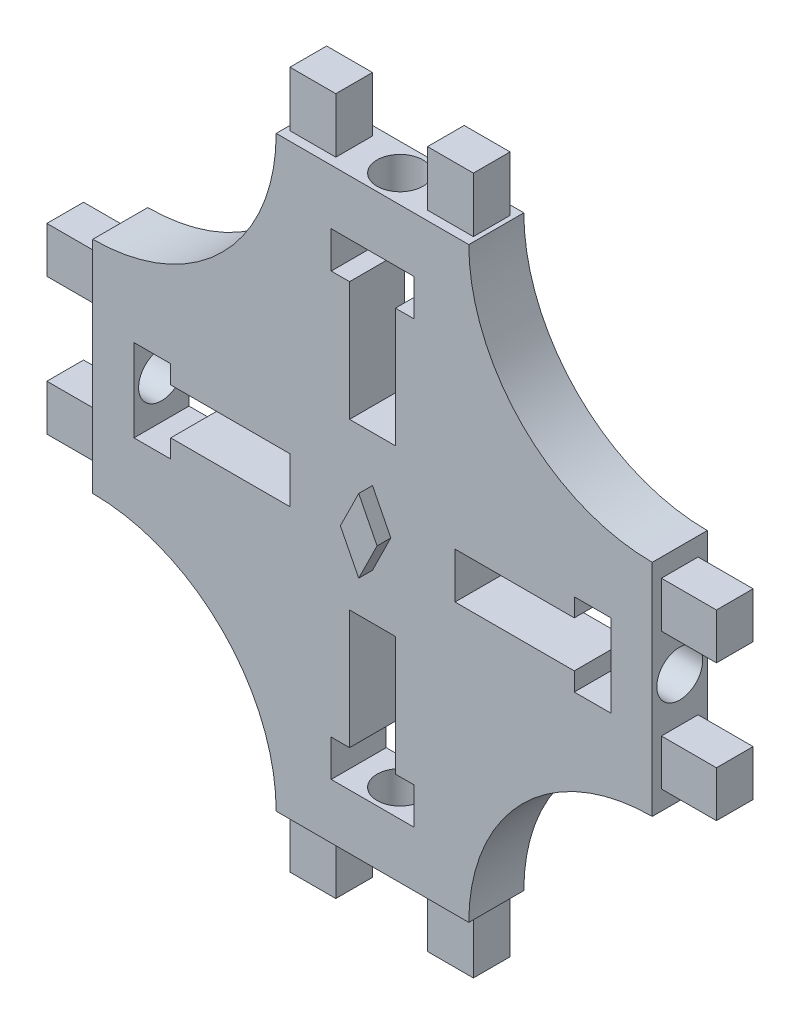
SolidWorks part; units mm, degrees
ref_plane "前视基准面" through (0, 0, 0) normal (0, 0, 1) x (1, 0, 0)
ref_plane "上视基准面" through (0, 0, 0) normal (0, 1, 0) x (1, 0, 0)
ref_plane "右视基准面" through (0, 0, 0) normal (1, 0, 0) x (0, 0, -1)
sketch "草图1" plane through (0, 0, 0) normal (0, 0, 1) x (1, 0, 0)
  line L0 (-15.25, 0) -> (15.25, 0) construction
  line L1 (-5, -16) -> (5, -16)
  line L2 (-15.25, -5) -> (-15.25, 5)
  line L3 (-5, 16) -> (5, 16)
  line L4 (15.25, -5) -> (15.25, 5)
  line L5 (-7.7137, -8.093) -> (7.7137, 8.093) construction
  line L6 (-7.7137, 8.093) -> (7.7137, -8.093) construction
  line L7 (0, 16) -> (0, -16) construction
  line L8 (-15.25, 0) -> (-15.25, 5)
  line L9 (-15.25, 0) -> (-15.25, -5)
  line L10 (0, 16) -> (-5, 16)
  line L11 (0, 16) -> (5, 16)
  line L12 (-2.25, 13) -> (0, 13)
  line L13 (0, -16) -> (-5, -16)
  line L14 (0, -16) -> (5, -16)
  line L15 (15.25, 0) -> (15.25, 5)
  line L16 (15.25, 0) -> (15.25, -5)
  line L17 (0, 13) -> (2.25, 13)
  line L18 (-2.25, 13) -> (-2.25, 11)
  line L19 (-2.25, 11) -> (2.25, 11)
  line L20 (2.25, 11) -> (2.25, 13)
  line L21 (-1.25, 11) -> (-1.25, 4.5)
  line L22 (-1.25, 4.5) -> (1.25, 4.5)
  line L23 (1.25, 4.5) -> (1.25, 11)
  line L24 (-1.25, -4.5) -> (1.25, -4.5)
  line L25 (-1.25, -11) -> (-1.25, -4.5)
  line L26 (1.25, -4.5) -> (1.25, -11)
  line L27 (-2.25, -11) -> (2.25, -11)
  line L28 (2.25, -11) -> (2.25, -13)
  line L29 (0, -13) -> (2.25, -13)
  line L30 (-2.25, -13) -> (0, -13)
  line L31 (-2.25, -13) -> (-2.25, -11)
  line L32 (4.5, 1.25) -> (11, 1.25)
  line L33 (4.5, -1.25) -> (4.5, 1.25)
  line L34 (11, -1.25) -> (4.5, -1.25)
  line L35 (11, -2.25) -> (11, 2.25)
  line L36 (13, -2.25) -> (11, -2.25)
  line L37 (11, 2.25) -> (13, 2.25)
  line L38 (13, 0) -> (13, 2.25)
  line L39 (13, -2.25) -> (13, 0)
  line L40 (-13, -2.25) -> (-13, 0)
  line L41 (-13, 0) -> (-13, 2.25)
  line L42 (-11, 2.25) -> (-13, 2.25)
  line L43 (-13, -2.25) -> (-11, -2.25)
  line L44 (-11, -2.25) -> (-11, 2.25)
  line L45 (-11, -1.25) -> (-4.5, -1.25)
  line L46 (-4.5, -1.25) -> (-4.5, 1.25)
  line L47 (-4.5, 1.25) -> (-11, 1.25)
  line L48 (-15.25, 5) -> (-15.25, 6)
  line L49 (-5.25, 16) -> (-5, 16)
  line L50 (5, 16) -> (5.25, 16)
  line L51 (15.25, 6) -> (15.25, 5)
  line L52 (15.25, -5) -> (15.25, -6)
  line L53 (5.25, -16) -> (5, -16)
  line L54 (-5, -16) -> (-5.25, -16)
  line L55 (-15.25, -6) -> (-15.25, -5)
  line L56 (-15.25, 5) -> (-15.25, 6)
  line L57 (-5, 16) -> (-5.25, 16)
  line L58 (5, 16) -> (5.25, 16)
  line L59 (15.25, 5) -> (15.25, 6)
  line L60 (15.25, -6) -> (15.25, -5)
  line L61 (5, -16) -> (5.25, -16)
  line L62 (-5, -16) -> (-5.25, -16)
  line L63 (-15.25, -5) -> (-15.25, -6)
  arc A4 (-15.25, 6) -> (-5.25, 16) centre (-15.25, 16) ccw
  arc A5 (5.25, 16) -> (15.25, 6) centre (15.25, 16) ccw
  arc A6 (15.25, -6) -> (5.25, -16) centre (15.25, -16) ccw
  arc A7 (-5.25, -16) -> (-15.25, -6) centre (-15.25, -16) ccw
  point P0 (0, 0)
  point P51 (0, 0)
  dimension "D11" = 20
  dimension "D19" = 20
  dimension "D20" = 20
  dimension "D21" = 20
  dimension "D2" = 32
  dimension "D3" = 5
  dimension "D4" = 5
  dimension "D5" = 5
  dimension "D6" = 5
  dimension "D7" = 5
  dimension "D8" = 5
  dimension "D9" = 5
  dimension "D10" = 5
  dimension "D12" = 30.5
  dimension "D13" = 2.25
  dimension "D14" = 2
  dimension "D15" = 3
  dimension "D16" = 2.5
  dimension "D17" = 6.5
  dimension "D18" = 2
extrude "凸台-拉伸2" add sketch "草图1" along normal blind 3
sketch "草图2" plane through (0, 16, 0) normal (0, 1, 0) x (1, 0, 0)
  line L0 (-5.25, 0) -> (5.25, -3) construction
  line L1 (5.25, 0) -> (-5.25, -3) construction
  circle A0 centre (0, -1.5) radius 1.25
  point P10 (0, 0)
  point P11 (0, 0)
  point P12 (-5.25, 0)
  point P14 (-5.25, -3)
  point P16 (5.25, 0)
  point P18 (5.25, -3)
  dimension "D1" = 2.5
extrude "切除-拉伸1" cut sketch "草图2" against normal blind 4
pattern_circular "阵列(圆周)1" count 4 over 360 about axis through (0, 0, 3) along (0, 0, 1) of "切除-拉伸1"
sketch "草图3" plane through (0, 0, 3) normal (0, 0, 1) x (1, 0, 0)
  line L0 (0, 0) -> (0, 2)
  line L1 (0, 0) -> (0, -2)
  line L2 (-1, -0.0251) -> (0, -2)
  line L3 (-1, -0.0251) -> (0, 2)
  line L4 (0, 2) -> (1, 0.0251)
  line L5 (1, 0.0251) -> (0, -2)
  line L6 (-1, -0.0251) -> (0, 0)
  line L7 (1, 0.0251) -> (0, 0)
  dimension "D1" = 1
  dimension "D2" = 2
extrude "凸台-拉伸3" add sketch "草图3" along normal blind 0.75 contours L7 L4 L0 | L3 L6 L0 | L6 L2 L1 | L5 L7 L1
sketch "草图4" plane through (0, 16, 0) normal (0, 1, 0) x (1, 0, 0)
  line L0 (0, -3.75) -> (0, -3) construction
  line L1 (2.5, -2.5) -> (5, -2.5)
  line L2 (2.5, -2.5) -> (2.5, -0.5)
  line L3 (2.5, -0.5) -> (5, -0.5)
  line L4 (5, -2.5) -> (5, -0.5)
  line L5 (2.5, -2.5) -> (5, -0.5) construction
  line L6 (2.5, -0.5) -> (5, -2.5) construction
  line L7 (-2.5, -2.5) -> (-5, -2.5)
  line L8 (-5, -2.5) -> (-5, -0.5)
  line L9 (-2.5, -2.5) -> (-2.5, -0.5)
  line L10 (-2.5, -0.5) -> (-5, -0.5)
  circle A0 centre (0, -1.5) radius 1.25 construction
  circle A1 centre (0, -1.5) radius 1.25
  point P3 (3.75, -1.5)
  point P8 (0, 0)
  dimension "D1" = 3.75
  dimension "D2" = 2
  dimension "D3" = 2.5
extrude "凸台-拉伸5" add sketch "草图4" along normal blind 3
pattern_linear "阵列(线性)1" count 2 spacing 35 along (0, -1, 0) of "凸台-拉伸5"
sketch "草图5" plane through (15.25, 0, 0) normal (1, 0, 0) x (0, 0, -1)
  line L0 (-3.75, 0.0251) -> (-3, 0.0251) construction
  line L1 (-2.5, 2.5) -> (-0.5, 2.5)
  line L2 (-2.5, 2.5) -> (-2.5, 5)
  line L3 (-2.5, 5) -> (-0.5, 5)
  line L4 (-0.5, 2.5) -> (-0.5, 5)
  line L5 (-2.5, 2.5) -> (-0.5, 5) construction
  line L6 (-2.5, 5) -> (-0.5, 2.5) construction
  line L7 (-2.5, -2.4498) -> (-0.5, -2.4498)
  line L8 (-0.5, -2.4498) -> (-0.5, -4.9498)
  line L9 (-2.5, -4.9498) -> (-0.5, -4.9498)
  line L10 (-2.5, -2.4498) -> (-2.5, -4.9498)
  circle A0 centre (-1.5, 0) radius 1.25 construction
  circle A1 centre (-1.5, 0) radius 1.25
  point P3 (-1.5, 3.75)
  dimension "D1" = 3.75
  dimension "D2" = 2
  dimension "D3" = 2.5
extrude "凸台-拉伸6" add sketch "草图5" along normal blind 3
pattern_linear "阵列(线性)2" count 2 spacing 33.5 along (-1, 0, 0) of "凸台-拉伸6"
